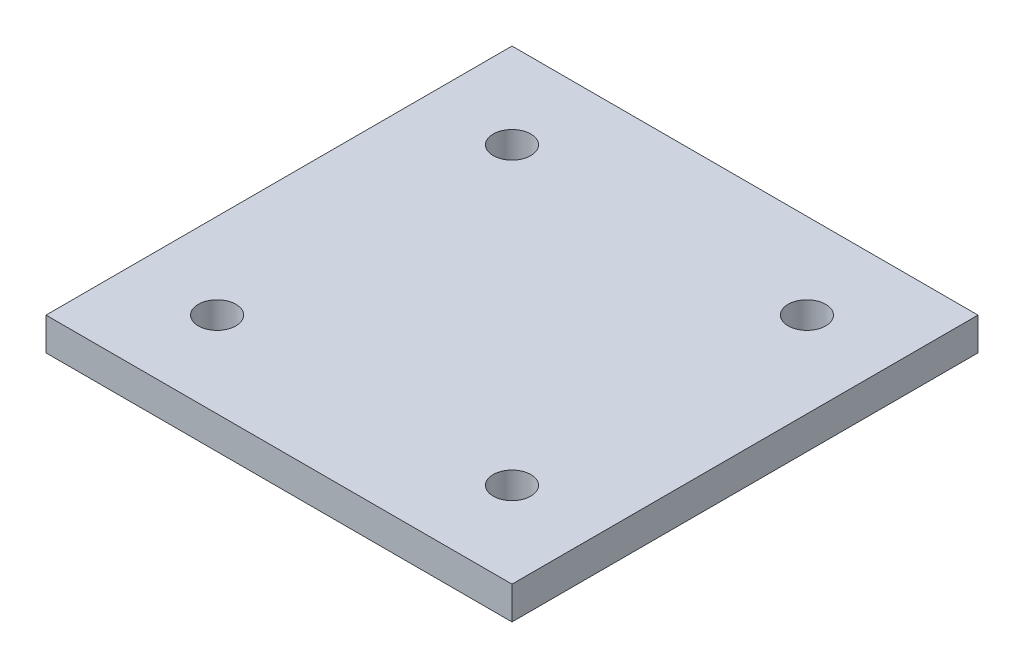
SolidWorks part; units mm, degrees
ref_plane "Front Plane" through (0, 0, 0) normal (0, 0, 1) x (1, 0, 0)
ref_plane "Top Plane" through (0, 0, 0) normal (0, 1, 0) x (1, 0, 0)
ref_plane "Right Plane" through (0, 0, 0) normal (1, 0, 0) x (0, 0, -1)
sketch "Sketch1" plane through (0, 0, 0) normal (0, 1, 0) x (1, 0, 0)
  line L0 (0, 14.2215) -> (0, -14.2215) construction
  line L1 (14.2215, -14.2215) -> (-14.2215, -14.2215)
  line L2 (14.2215, -14.2215) -> (14.2215, 14.2215)
  line L3 (14.2215, 14.2215) -> (-14.2215, 14.2215)
  line L4 (-14.2215, -14.2215) -> (-14.2215, 14.2215)
  line L5 (14.2215, -14.2215) -> (-14.2215, 14.2215) construction
  line L6 (14.2215, 14.2215) -> (-14.2215, -14.2215) construction
  line L7 (-14.2215, 0) -> (14.2215, 0) construction
  circle A0 centre (-9, 9) radius 1.1462
  circle A1 centre (9, 9) radius 1.1462
  circle A2 centre (9, -9) radius 1.1462
  circle A3 centre (-9, -9) radius 1.1462
  point P0 (0, 0)
  dimension "D2" = 18
extrude "Boss-Extrude1" add sketch "Sketch1" along normal blind 2
